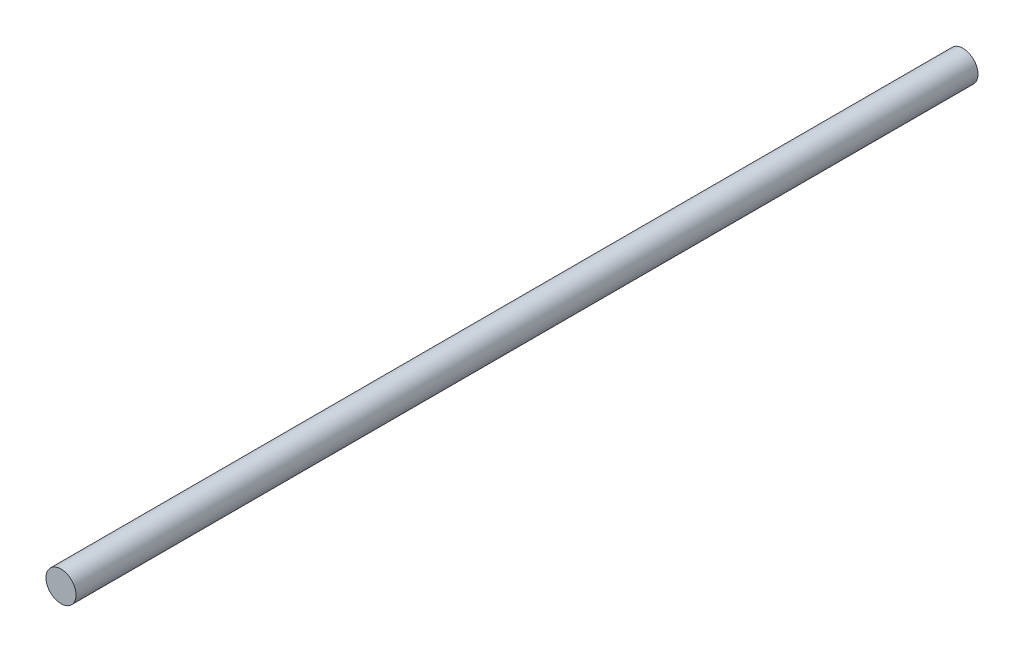
SolidWorks part; units mm, degrees
ref_plane "Front Plane" through (0, 0, 0) normal (0, 0, 1) x (1, 0, 0)
ref_plane "Top Plane" through (0, 0, 0) normal (0, 1, 0) x (1, 0, 0)
ref_plane "Right Plane" through (0, 0, 0) normal (1, 0, 0) x (0, 0, -1)
sketch "Sketch1" plane through (0, 0, 0) normal (0, 0, 1) x (1, 0, 0)
  circle A0 centre (0, 0) radius 2
  dimension "D1" = 4
extrude "Boss-Extrude1" add sketch "Sketch1" along normal blind 120
